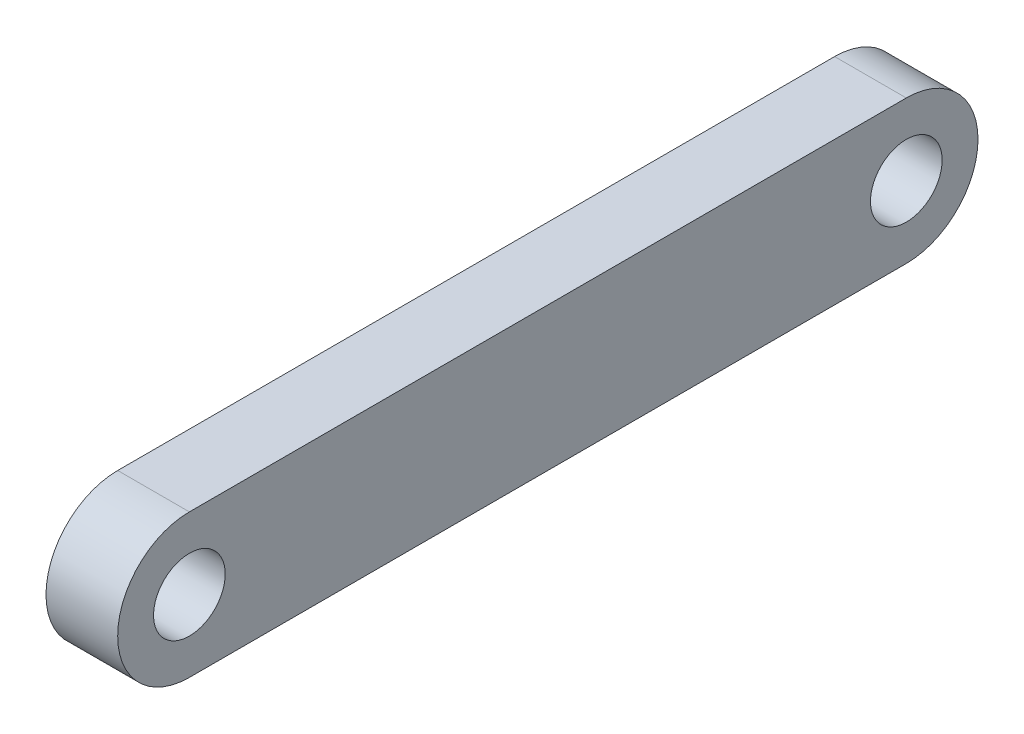
SolidWorks part; units mm, degrees
material "普通碳钢"
ref_plane "前视基准面" through (0, 0, 0) normal (0, 0, 1) x (1, 0, 0)
ref_plane "上视基准面" through (0, 0, 0) normal (0, 1, 0) x (1, 0, 0)
ref_plane "右视基准面" through (0, 0, 0) normal (1, 0, 0) x (0, 0, -1)
sketch "草图1" plane through (0, 0, 0) normal (1, 0, 0) x (0, 0, -1)
  line L0 (0, 0) -> (80, 0) construction
  line L1 (0, 8) -> (80, 8)
  line L2 (0, -8) -> (80, -8)
  circle A0 centre (0, 0) radius 4
  circle A1 centre (80, 0) radius 4
  arc A2 (0, 8) -> (0, -8) centre (0, 0) ccw
  arc A3 (80, -8) -> (80, 8) centre (80, 0) ccw
  dimension "D1" = 8
  dimension "D2" = 8
  dimension "D3" = 16
  dimension "D4" = 16
  dimension "D5" = 80
extrude "凸台-拉伸1" add sketch "草图1" along normal blind 8
